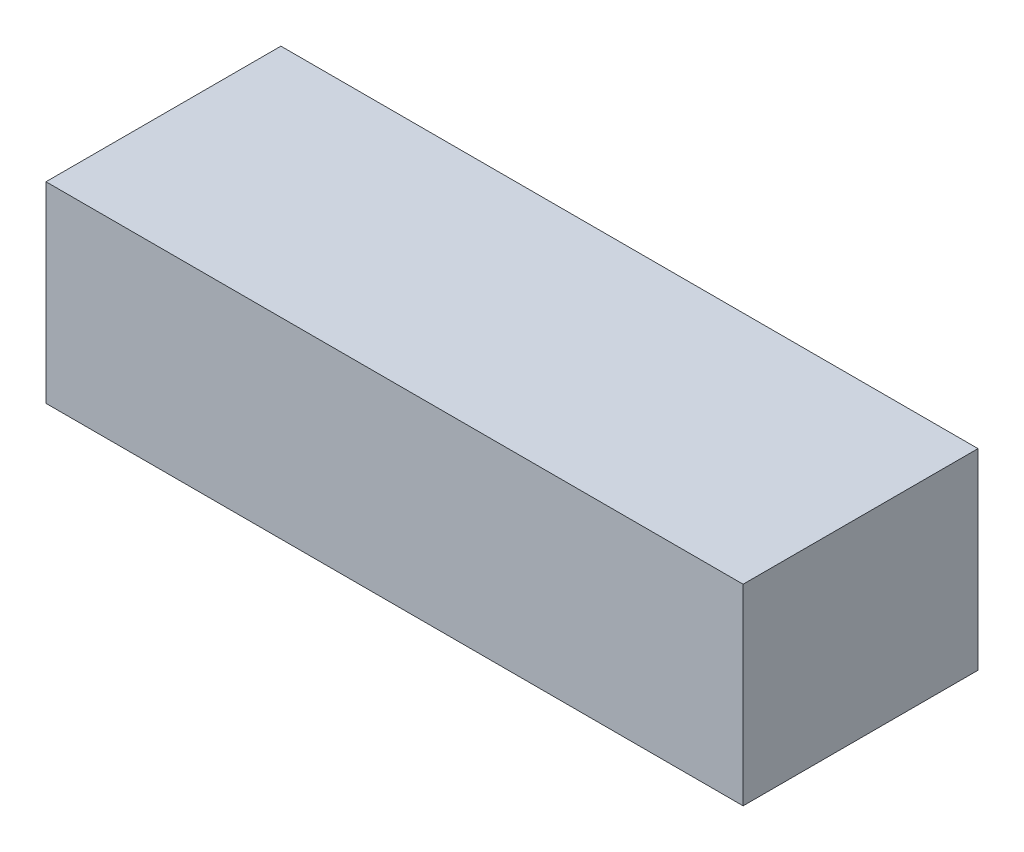
SolidWorks part; units mm, degrees
ref_plane "Ebene vorne" through (0, 0, 0) normal (0, 0, 1) x (1, 0, 0)
ref_plane "Ebene oben" through (0, 0, 0) normal (0, 1, 0) x (1, 0, 0)
ref_plane "Ebene rechts" through (0, 0, 0) normal (1, 0, 0) x (0, 0, -1)
sketch "Skizze1" plane through (0, 0, 0) normal (0, 1, 0) x (1, 0, 0)
  line L1 (-69, 0) -> (69, 0)
  line L2 (-69, 0) -> (-69, 46.5)
  line L3 (-69, 46.5) -> (69, 46.5)
  line L4 (69, 0) -> (69, 46.5)
  point P10 (0, 0)
  dimension "D1" = 138
  dimension "D2" = 46.5
extrude "Aufsatz-Linear austragen1" add sketch "Skizze1" along normal blind 38
